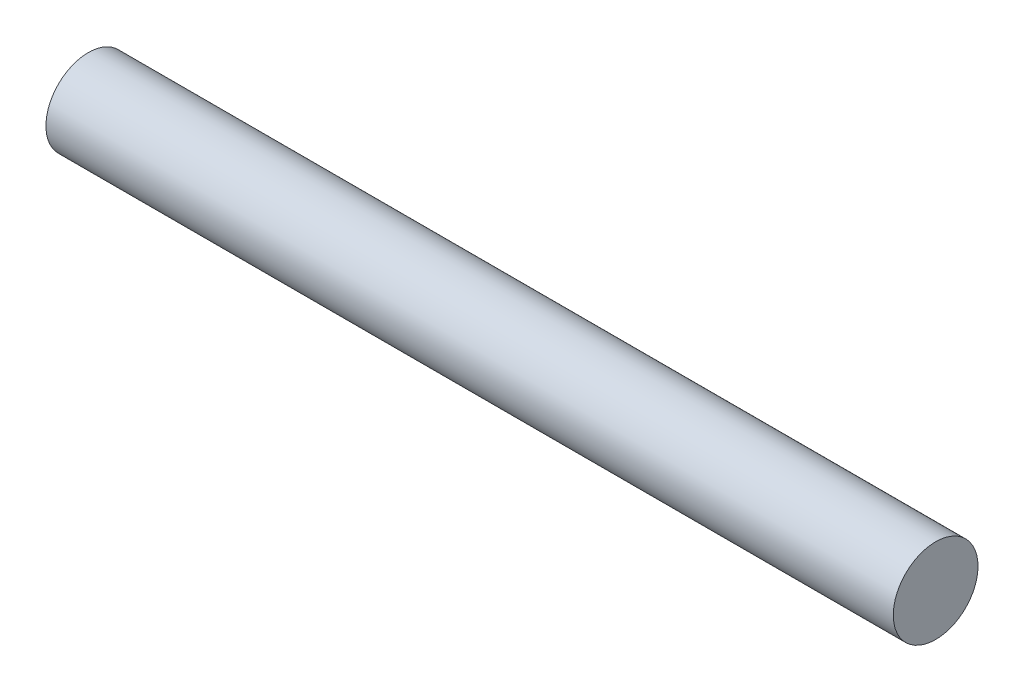
SolidWorks part; units mm, degrees
ref_plane "Front Plane" through (0, 0, 0) normal (0, 0, 1) x (1, 0, 0)
ref_plane "Top Plane" through (0, 0, 0) normal (0, 1, 0) x (1, 0, 0)
ref_plane "Right Plane" through (0, 0, 0) normal (1, 0, 0) x (0, 0, -1)
sketch "Sketch1" plane through (0, 0, 0) normal (1, 0, 0) x (0, 0, -1)
  circle A0 centre (0, 0) radius 2.5
  dimension "D1" = 5
extrude "Boss-Extrude1" add sketch "Sketch1" along normal blind 50
